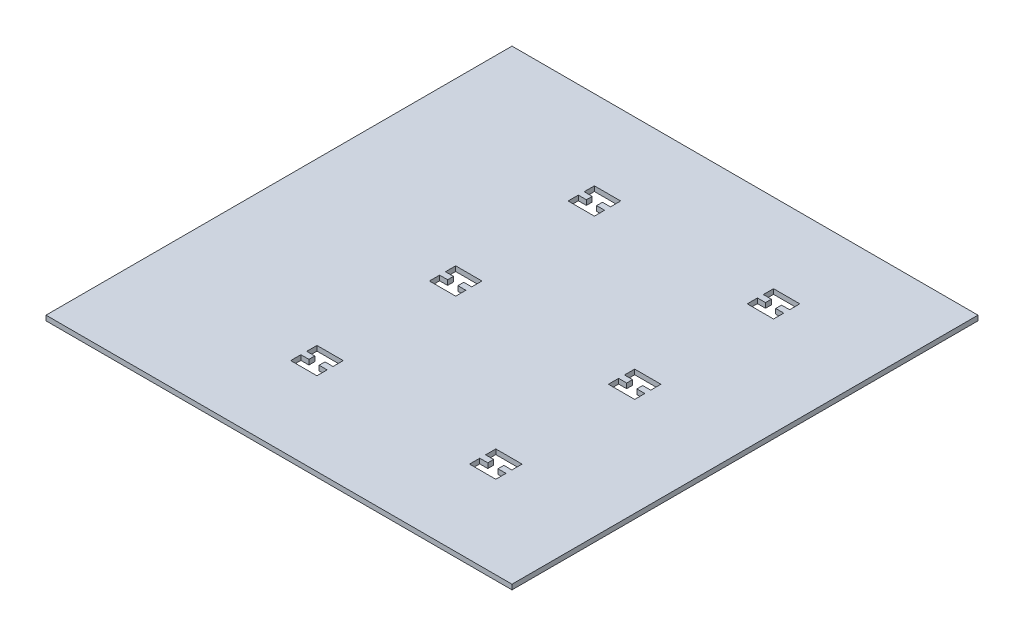
SolidWorks part; units mm, degrees
ref_plane "Front Plane" through (0, 0, 0) normal (0, 0, 1) x (1, 0, 0)
ref_plane "Top Plane" through (0, 0, 0) normal (0, 1, 0) x (1, 0, 0)
ref_plane "Right Plane" through (0, 0, 0) normal (1, 0, 0) x (0, 0, -1)
sketch "Sketch1" plane through (0, 0, 0) normal (0, 1, 0) x (1, 0, 0)
  line L1 (-149.225, -149.225) -> (149.225, -149.225)
  line L2 (-149.225, -149.225) -> (-149.225, 149.225)
  line L3 (-149.225, 149.225) -> (149.225, 149.225)
  line L4 (149.225, -149.225) -> (149.225, 149.225)
  line L5 (-149.225, -149.225) -> (149.225, 149.225) construction
  line L6 (-149.225, 149.225) -> (149.225, -149.225) construction
  point P0 (0, 0)
  point P6 (0, 0)
  point P7 (0, 0)
  point P8 (0, 0)
  point P9 (152.4, -152.4)
  point P10 (0, 0)
  line B0 (-45.6628, -79.2598) -> (-45.6628, -85.7998)
  line B1 (-45.6628, -85.7998) -> (-40.519, -85.7998)
  line B2 (-40.519, -85.7998) -> (-40.519, -89.5473)
  line B3 (-40.519, -89.5473) -> (-45.6628, -89.5473)
  line B4 (-45.6628, -89.5473) -> (-45.6628, -96.0873)
  line B5 (-45.6628, -96.0873) -> (-28.8353, -96.0873)
  line B6 (-28.8353, -96.0873) -> (-28.8353, -89.5473)
  line B7 (-28.8353, -89.5473) -> (-33.979, -89.5473)
  line B8 (-33.979, -89.5473) -> (-33.979, -85.7998)
  line B9 (-33.979, -85.7998) -> (-28.8353, -85.7998)
  line B10 (-28.8353, -85.7998) -> (-28.8353, -79.2598)
  line B11 (-28.8353, -79.2598) -> (-45.6628, -79.2598)
  line B12 (-45.3862, 9.3118) -> (-45.3862, 2.7718)
  line B13 (-45.3862, 2.7718) -> (-40.2425, 2.7718)
  line B14 (-40.2425, 2.7718) -> (-40.2425, -0.9757)
  line B15 (-40.2425, -0.9757) -> (-45.3862, -0.9757)
  line B16 (-45.3862, -0.9757) -> (-45.3862, -7.5157)
  line B17 (-45.3862, -7.5157) -> (-28.5587, -7.5157)
  line B18 (-28.5587, -7.5157) -> (-28.5587, -0.9757)
  line B19 (-28.5587, -0.9757) -> (-33.7025, -0.9757)
  line B20 (-33.7025, -0.9757) -> (-33.7025, 2.7718)
  line B21 (-33.7025, 2.7718) -> (-28.5587, 2.7718)
  line B22 (-28.5587, 2.7718) -> (-28.5587, 9.3118)
  line B23 (-28.5587, 9.3118) -> (-45.3862, 9.3118)
  line B24 (-45.3465, 98.1141) -> (-45.3465, 91.5741)
  line B25 (-45.3465, 91.5741) -> (-40.2027, 91.5741)
  line B26 (-40.2027, 91.5741) -> (-40.2027, 87.8266)
  line B27 (-40.2027, 87.8266) -> (-45.3465, 87.8266)
  line B28 (-45.3465, 87.8266) -> (-45.3465, 81.2866)
  line B29 (-45.3465, 81.2866) -> (-28.519, 81.2866)
  line B30 (-28.519, 81.2866) -> (-28.519, 87.8266)
  line B31 (-28.519, 87.8266) -> (-33.6627, 87.8266)
  line B32 (-33.6627, 87.8266) -> (-33.6627, 91.5741)
  line B33 (-33.6627, 91.5741) -> (-28.519, 91.5741)
  line B34 (-28.519, 91.5741) -> (-28.519, 98.1141)
  line B35 (-28.519, 98.1141) -> (-45.3465, 98.1141)
  line B36 (69.0699, 98.4342) -> (69.0699, 91.8942)
  line B37 (69.0699, 91.8942) -> (74.2136, 91.8942)
  line B38 (74.2136, 91.8942) -> (74.2136, 88.1467)
  line B39 (74.2136, 88.1467) -> (69.0699, 88.1467)
  line B40 (69.0699, 88.1467) -> (69.0699, 81.6067)
  line B41 (69.0699, 81.6067) -> (85.8974, 81.6067)
  line B42 (85.8974, 81.6067) -> (85.8974, 88.1467)
  line B43 (85.8974, 88.1467) -> (80.7536, 88.1467)
  line B44 (80.7536, 88.1467) -> (80.7536, 91.8942)
  line B45 (80.7536, 91.8942) -> (85.8974, 91.8942)
  line B46 (85.8974, 91.8942) -> (85.8974, 98.4342)
  line B47 (85.8974, 98.4342) -> (69.0699, 98.4342)
  line B48 (69.1981, 9.3678) -> (69.1981, 2.8278)
  line B49 (69.1981, 2.8278) -> (74.3419, 2.8278)
  line B50 (74.3419, 2.8278) -> (74.3419, -0.9197)
  line B51 (74.3419, -0.9197) -> (69.1981, -0.9197)
  line B52 (69.1981, -0.9197) -> (69.1981, -7.4597)
  line B53 (69.1981, -7.4597) -> (86.0256, -7.4597)
  line B54 (86.0256, -7.4597) -> (86.0256, -0.9197)
  line B55 (86.0256, -0.9197) -> (80.8819, -0.9197)
  line B56 (80.8819, -0.9197) -> (80.8819, 2.8278)
  line B57 (80.8819, 2.8278) -> (86.0256, 2.8278)
  line B58 (86.0256, 2.8278) -> (86.0256, 9.3678)
  line B59 (86.0256, 9.3678) -> (69.1981, 9.3678)
  line B60 (69.0124, -79.3922) -> (69.0124, -85.9322)
  line B61 (69.0124, -85.9322) -> (74.1562, -85.9322)
  line B62 (74.1562, -85.9322) -> (74.1562, -89.6797)
  line B63 (74.1562, -89.6797) -> (69.0124, -89.6797)
  line B64 (69.0124, -89.6797) -> (69.0124, -96.2197)
  line B65 (69.0124, -96.2197) -> (85.8399, -96.2197)
  line B66 (85.8399, -96.2197) -> (85.8399, -89.6797)
  line B67 (85.8399, -89.6797) -> (80.6962, -89.6797)
  line B68 (80.6962, -89.6797) -> (80.6962, -85.9322)
  line B69 (80.6962, -85.9322) -> (85.8399, -85.9322)
  line B70 (85.8399, -85.9322) -> (85.8399, -79.3922)
  line B71 (85.8399, -79.3922) -> (69.0124, -79.3922)
  dimension "D1" = 298.45
  dimension "D2" = 298.45
sketch_block_instance "Block1-1"
sketch_block "Block1"
sketch_block_instance "Block1-3"
sketch_block_instance "Block1-4"
sketch_block_instance "Block1-5"
sketch_block_instance "Block1-6"
sketch_block_instance "Block1-7"
extrude "Boss-Extrude1" add sketch "Sketch1" along normal blind 3.175
